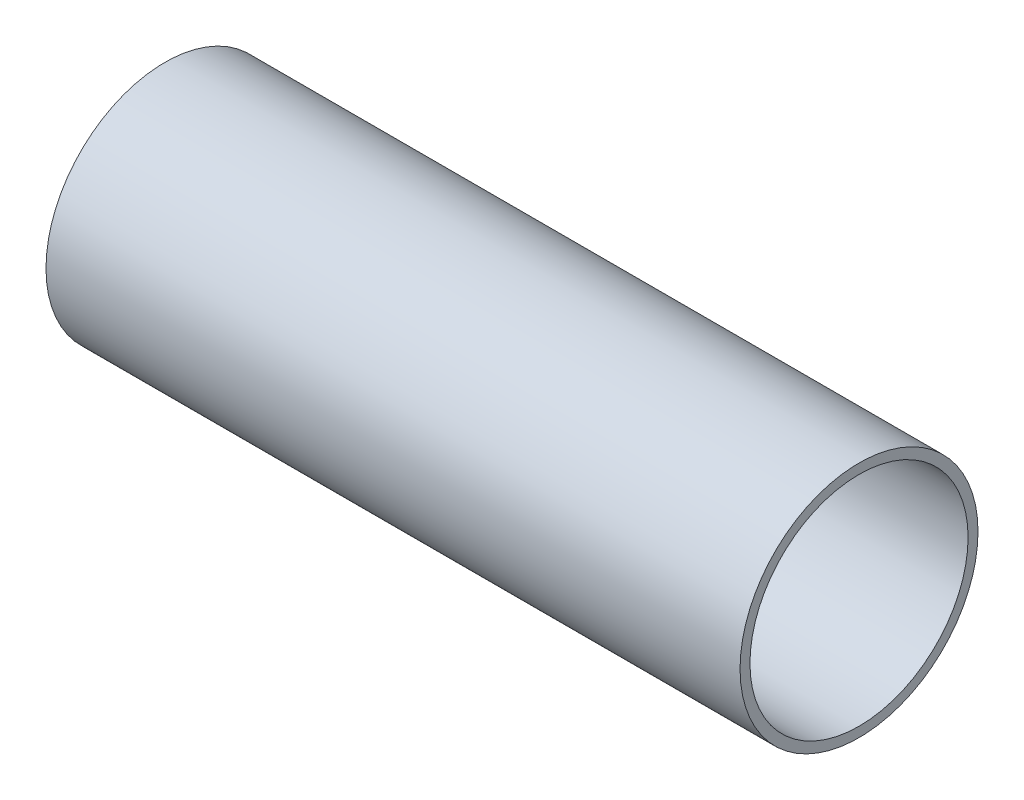
SolidWorks part; units mm, degrees
ref_plane "Front" through (0, 0, 0) normal (0, 0, 1) x (1, 0, 0)
ref_plane "Top" through (0, 0, 0) normal (0, 1, 0) x (1, 0, 0)
ref_plane "Right" through (0, 0, 0) normal (1, 0, 0) x (0, 0, -1)
sketch "Эскиз1" plane through (0, 0, 0) normal (1, 0, 0) x (0, 0, -1)
  circle A0 centre (0, 0) radius 60
  circle A1 centre (0, 0) radius 55
  dimension "D1" = 120
  dimension "D2" = 5
extrude "Бобышка-Вытянуть1" add sketch "Эскиз1" along normal blind 350
